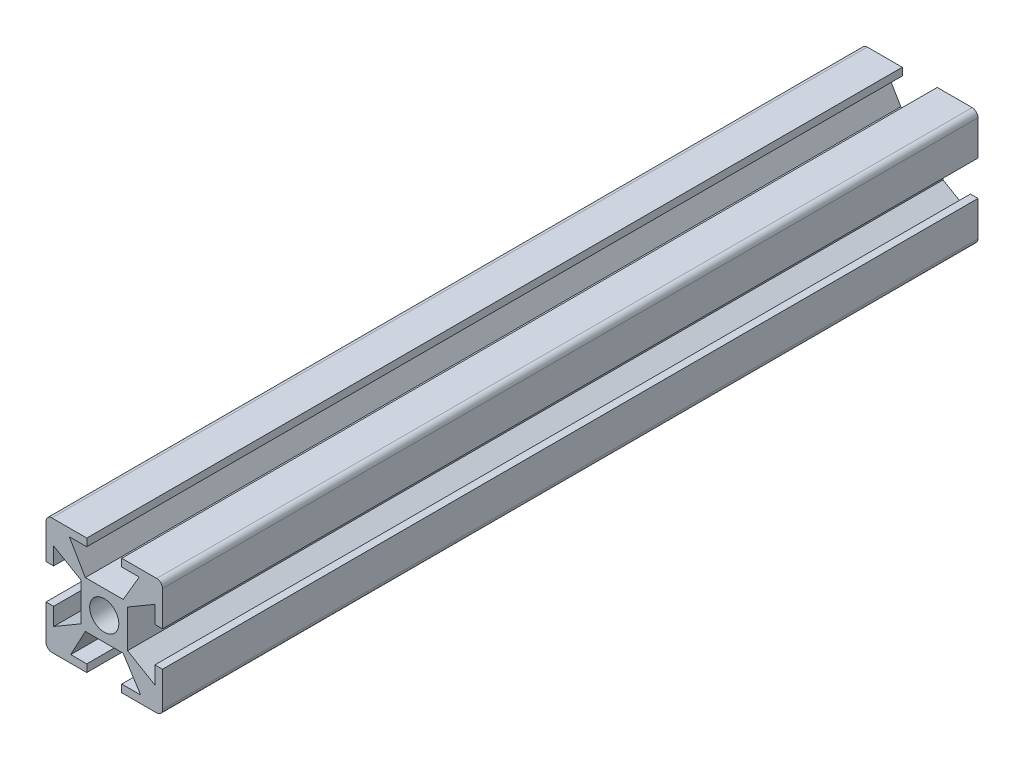
SolidWorks part; units mm, degrees
ref_plane "Alzado" through (0, 0, 0) normal (0, 0, 1) x (1, 0, 0)
ref_plane "Planta" through (0, 0, 0) normal (0, 1, 0) x (1, 0, 0)
ref_plane "Vista lateral" through (0, 0, 0) normal (1, 0, 0) x (0, 0, -1)
sketch "Croquis1" plane through (0, 0, 0) normal (0, 0, 1) x (1, 0, 0)
  line L0 (-3, 10) -> (3, 10)
  line L1 (-9, 10) -> (9, 10)
  line L2 (-10, 9) -> (-10, -9)
  line L3 (-9, -10) -> (9, -10)
  line L4 (10, 9) -> (10, -9)
  line L5 (-10, 10) -> (10, -10) construction
  line L6 (-10, -10) -> (10, 10) construction
  line L7 (-4, 4) -> (4, 4)
  line L8 (-4, 4) -> (-4, -4)
  line L9 (-4, -4) -> (4, -4)
  line L10 (4, 4) -> (4, -4)
  line L11 (-4, 4) -> (4, -4) construction
  line L12 (-4, -4) -> (4, 4) construction
  line L13 (3, 10) -> (3, 8.7)
  line L14 (-3.25, 4) -> (3.25, 4)
  line L15 (0, 10) -> (0, -10) construction
  line L16 (-10, 0) -> (10, 0) construction
  line L20 (-3, 10) -> (-3, 8.7)
  line L22 (3, -10) -> (3, -8.7)
  line L23 (-3, -10) -> (3, -10)
  line L24 (-3, -10) -> (-3, -8.7)
  line L25 (-5.75, -8.7) -> (-3, -8.7)
  line L26 (-5.75, -8.7) -> (-3.25, -4)
  line L27 (-3.25, -4) -> (3.25, -4)
  line L28 (6.25, -8.7) -> (3.25, -4)
  line L29 (3, -8.7) -> (6.25, -8.7)
  line L30 (-10, 3) -> (-10, -3)
  line L31 (-4, 3.25) -> (-4, -3.25)
  line L32 (-10, 3) -> (-8.7, 3)
  line L33 (-8.7, -6) -> (-8.7, -3)
  line L34 (-8.7, 6) -> (-4, 3.25)
  line L35 (-8.7, -6) -> (-4, -3.25)
  line L36 (-10, -3) -> (-8.7, -3)
  line L37 (-8.7, 3) -> (-8.7, 6)
  line L38 (8.7, -6) -> (4, -3.25)
  line L39 (4, 3.25) -> (4, -3.25)
  line L40 (8.7, 6) -> (4, 3.25)
  line L41 (8.7, 3) -> (8.7, 6)
  line L42 (10, 3) -> (8.7, 3)
  line L43 (10, 3) -> (10, -3)
  line L44 (10, -3) -> (8.7, -3)
  line L45 (8.7, -6) -> (8.7, -3)
  line L46 (-6, 8.7) -> (-3, 8.7)
  line L47 (-6, 8.7) -> (-3.25, 4)
  line L48 (6, 8.7) -> (3.25, 4)
  line L49 (3, 8.7) -> (6, 8.7)
  circle A0 centre (0, 0) radius 2.5
  arc A1 (-10, -9) -> (-9, -10) centre (-9, -9) ccw
  arc A2 (9, -10) -> (10, -9) centre (9, -9) ccw
  arc A3 (9, 10) -> (10, 9) centre (9, 9) cw
  arc A4 (-9, 10) -> (-10, 9) centre (-9, 9) ccw
  point P0 (0, 0)
  point P6 (0, 0)
  point P14 (0, 10)
  point P18 (0, 4)
  point P25 (0, 8.7)
  point P37 (-10, 0)
  point P40 (-4, 0)
  point P44 (-8.7, 0)
  point P56 (0, 8.7)
  dimension "D12" = 5
  dimension "D13" = 1
  dimension "D1" = 20
  dimension "D2" = 20
  dimension "D3" = 8
  dimension "D4" = 8
  dimension "D5" = 6
  dimension "D6" = 6.5
  dimension "D7" = 12
  dimension "D8" = 6.5
  dimension "D9" = 6
  dimension "D10" = 1.3
  dimension "D11" = 12
extrude "Saliente-Extruir4" add sketch "Croquis1" along normal blind 140 contours L1 A4 L2 L32 L37 L34 L8 L7 L47 L46 L20 | A3 L1 L13 L49 L48 L7 L10 L40 L41 L42 L4 | L3 A2 L4 L44 L45 L38 L10 L9 L28 L29 L22 | L2 A1 L3 L24 L25 L26 L9 L8 L35 L33 L36 | L10 L7 L8 L9 A0
